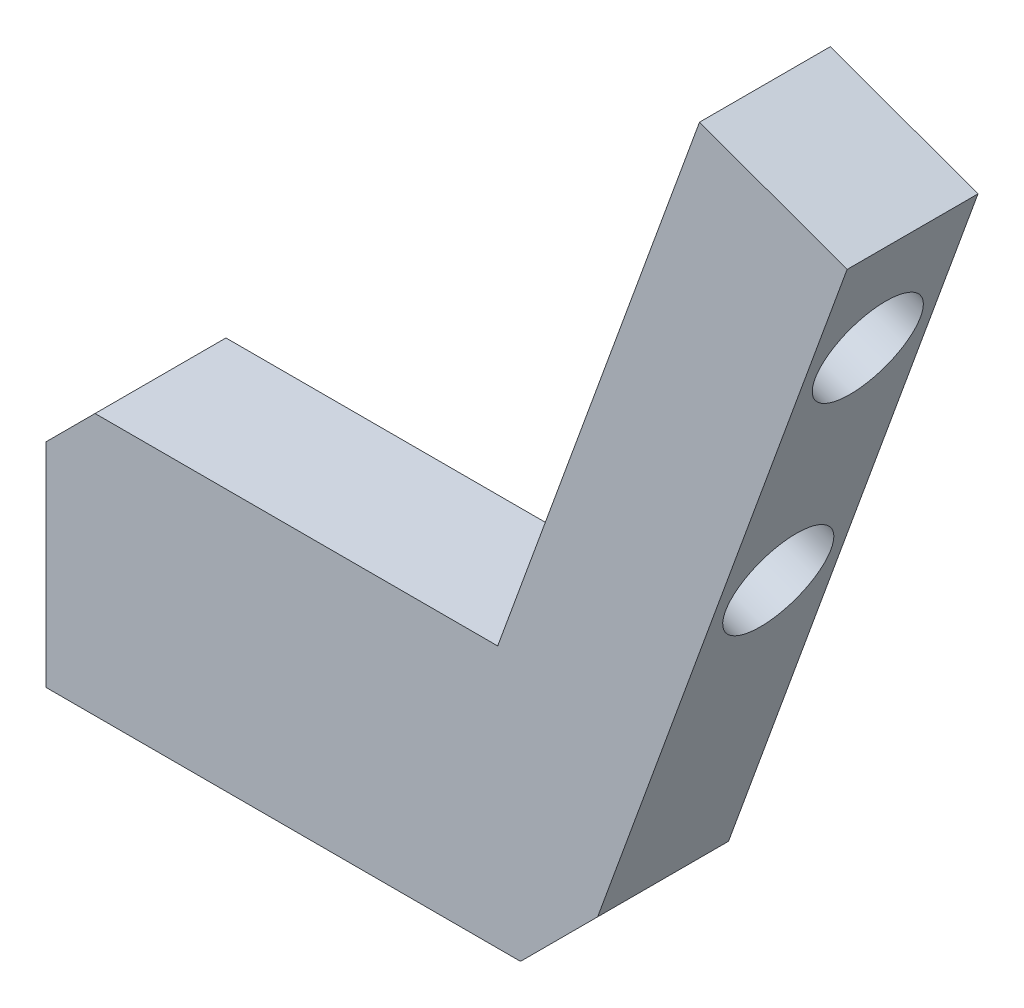
SolidWorks part; units mm, degrees
material "5052-O"
ref_plane "Front Plane" through (0, 0, 0) normal (0, 0, 1) x (1, 0, 0)
ref_plane "Top Plane" through (0, 0, 0) normal (0, 1, 0) x (1, 0, 0)
ref_plane "Right Plane" through (0, 0, 0) normal (1, 0, 0) x (0, 0, -1)
sketch "Sketch1" plane through (0, 0, 0) normal (0, 0, 1) x (1, 0, 0)
  line L0 (-25.4, 0) -> (0, 0)
  line L1 (0, 0) -> (13.4653, 36.9957)
  line L4 (-25.4, 12.7) -> (-25.4, 0)
  line L5 (13.4653, 36.9957) -> (6.3049, 39.6019)
  line L6 (6.3049, 39.6019) -> (-3.4866, 12.7)
  line L9 (-25.4, 12.7) -> (-3.4866, 12.7)
  dimension "D1" = 70
  dimension "D2" = 12.7
  dimension "D3" = 25.4
  dimension "D4" = 7.62
  dimension "D5" = 39.37
extrude "Boss-Extrude1" add sketch "Sketch1" along normal mid plane 6.35
sketch "Sketch2" plane through (0, 0, 0) normal (0, -1, 0) x (1, 0, 0)
  line L0 (-25.4, 0) -> (-22.225, 0) construction
  line L1 (-25.4, 3.175) -> (-25.4, -3.175) construction
  line L2 (-22.225, 0) -> (-9.525, 0) construction
  point P3 (-22.225, 0)
  point P4 (-9.525, 0)
  dimension "D2" = 3.175
  dimension "D1" = 12.7
hole_wizard "Tap Drill for #10-24 Tap1" positions "Sketch3" profile "Sketch4" hole size "#10-24" standard "ANSI Inch"
sketch "Sketch3" plane through (0, 0, 0) normal (0, -1, 0) x (-1, 0, 0)
  point P0 (22.225, 0)
  point P3 (9.525, 0)
sketch "Sketch4" plane through (-22.225, 0, 0) normal (1, 0, 0) x (0, 0, -1)
  line L0 (0, 0) -> (0, 11.3008)
  line L1 (0, 11.3008) -> (1.8986, 10.16)
  line L2 (1.8986, 10.16) -> (1.8986, 0)
  line L5 (1.8986, 0) -> (0, 0)
  line L10 (0, 11.3008) -> (-1.8987, 10.16) construction
  line L11 (0, -6.35) -> (0, 107.95) construction
  dimension "Hole Dia." = 3.7973
  dimension "Hole Depth" = 10.16
  dimension "Drill Angle" = 118
ref_plane "Plane1" through (0, 0, 0) normal (-0.8192, -0.5736, 0) x (0, 0, 1)
chamfer "Chamfer1" distance 2.38 angle 45 2 edges at (0, 0, 0) (-25.4, 12.7, 0)
sketch "Sketch5" plane through (0, 0, 0) normal (0.9397, -0.342, 0) x (0, 0, -1)
  line L0 (0, 39.37) -> (0, 33.02) construction
  line L1 (-3.175, 39.37) -> (3.175, 39.37) construction
  line L2 (0, 33.02) -> (0, 20.32) construction
  point P7 (0, 20.32)
  point P8 (0, 33.02)
  dimension "D1" = 6.35
  dimension "D2" = 12.7
hole_wizard "#10 Clearance Hole1" positions "Sketch6" profile "Sketch7" hole size "#10" standard "ANSI Inch"
sketch "Sketch6" plane through (0, 0, 0) normal (0.9397, -0.342, 0) x (0, 0, -1)
  point P0 (0, 33.02)
  point P3 (0, 20.32)
sketch "Sketch7" plane through (11.2935, 31.0287, 0) normal (0, 0, 1) x (0.342, 0.9397, 0)
  line L0 (0, 0) -> (0, 14.2338)
  line L1 (0, 14.2338) -> (2.5527, 12.7)
  line L2 (2.5527, 12.7) -> (2.5527, 0)
  line L5 (2.5527, 0) -> (0, 0)
  line L10 (0, 14.2338) -> (-2.5527, 12.7) construction
  line L11 (0, -6.35) -> (0, 107.95) construction
  dimension "Hole Dia." = 5.1054
  dimension "Hole Depth" = 12.7
  dimension "Drill Angle" = 118
